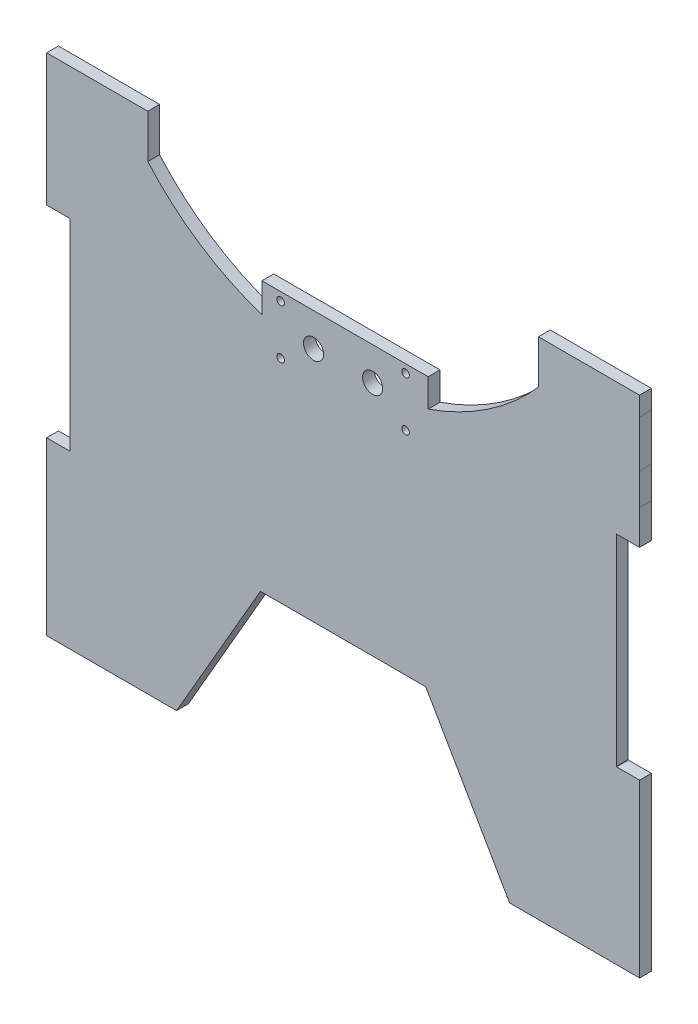
SolidWorks part; units mm, degrees
ref_plane "Front Plane" through (0, 0, 0) normal (0, 0, 1) x (1, 0, 0)
ref_plane "Top Plane" through (0, 0, 0) normal (0, 1, 0) x (1, 0, 0)
ref_plane "Right Plane" through (0, 0, 0) normal (1, 0, 0) x (0, 0, -1)
sketch "Sketch1" plane through (0, 0, 0) normal (0, 0, 1) x (1, 0, 0)
  line L0 (-91.7228, 104.3562) -> (-126.4585, 104.3562)
  line L1 (-126.4585, 104.3562) -> (-126.4753, 84.6144)
  line L2 (-126.4753, 84.6144) -> (-126.4804, 71.1807)
  line L3 (-126.4804, 71.1807) -> (-126.4807, 56.5595)
  line L4 (-126.4807, 56.5595) -> (-116.6382, 56.5595)
  line L5 (-116.6382, 56.5595) -> (-116.6382, -28.7876)
  line L6 (-116.6382, -28.7876) -> (-126.4819, -28.7876)
  line L7 (-126.4819, -28.7876) -> (-126.4819, -101.3441)
  line L8 (-126.4819, -101.3441) -> (-71.449, -101.3441)
  line L9 (-71.449, -101.3441) -> (-35.9282, -39.8203)
  line L10 (-35.9282, -39.8203) -> (34.0758, -39.8203)
  line L11 (34.0758, -39.8203) -> (69.5966, -101.3441)
  line L12 (69.5966, -101.3441) -> (124.6295, -101.3441)
  line L13 (124.6295, -101.3441) -> (124.6295, -28.7876)
  line L14 (124.6295, -28.7876) -> (114.9127, -28.7876)
  line L15 (114.7857, -28.6606) -> (114.7857, 56.4325)
  line L16 (114.9127, 56.5595) -> (124.6283, 56.5595)
  line L17 (124.6283, 56.5595) -> (124.6279, 71.1707)
  line L18 (124.6279, 71.1707) -> (124.6228, 84.6244)
  line L19 (124.6228, 84.6244) -> (124.6061, 104.3562)
  line L20 (124.6061, 104.3562) -> (89.8704, 104.3562)
  line L21 (35.0896, 62.5159) -> (35.0896, 40.386)
  line L22 (35.0896, 40.386) -> (-35.3107, 40.386)
  line L23 (-35.3107, 40.386) -> (-35.3107, 61.9649)
  arc A0 (-91.7228, 104.3562) -> (-35.3107, 61.9649) centre (-0.9262, 166.4527) ccw
  arc A1 (114.7857, -28.6606) -> (114.9127, -28.7876) centre (114.9127, -28.6606) ccw
  arc A2 (114.9127, 56.5595) -> (114.7857, 56.4325) centre (114.9127, 56.4325) ccw
  arc A3 (35.0896, 62.5159) -> (89.8704, 104.3562) centre (-0.9262, 166.4527) ccw
extrude "Boss-Extrude1" add sketch "Sketch1" along normal blind 5
sketch "Sketch2" plane through (0, 0, 5) normal (0, 0, 1) x (1, 0, 0)
  line L1 (-35.3107, 40.386) -> (35.0896, 40.386)
  line L2 (-35.3107, 40.386) -> (-35.3107, 74.386)
  line L3 (-35.3107, 74.386) -> (35.0896, 74.386)
  line L4 (35.0896, 40.386) -> (35.0896, 74.386)
  line L5 (-35.3107, 40.386) -> (35.0896, 74.386) construction
  line L6 (-35.3107, 74.386) -> (35.0896, 40.386) construction
  circle A0 centre (-27.3907, 70.8504) radius 1.6
  circle A1 centre (-27.3907, 49.9215) radius 1.6
  circle A2 centre (25.5383, 49.9215) radius 1.6
  circle A3 centre (25.5383, 70.8504) radius 1.6
  circle A4 centre (-13.4262, 60.386) radius 4.25
  circle A5 centre (11.5738, 60.386) radius 4.25
  point P4 (-0.1106, 57.386)
  dimension "D1" = 8.5
extrude "Boss-Extrude2" add sketch "Sketch2" against normal blind 5
sketch "Sketch3" plane through (0, 0, 5) normal (0, 0, 1) x (1, 0, 0)
  line L0 (-126.4585, 104.3562) -> (-126.4585, 112.386)
  line L1 (-91.7228, 104.3562) -> (-91.7228, 112.386)
  line L2 (-126.4585, 112.386) -> (-66.5142, 112.386) construction
  line L3 (-91.7228, 112.386) -> (-126.4585, 112.386)
  line L4 (-0.9262, 108.4013) -> (-0.9262, 130.7418) construction
  line L5 (89.8704, 104.3562) -> (124.6061, 104.3562)
  line L6 (89.8704, 112.386) -> (124.6061, 112.386)
  line L7 (89.8704, 104.3562) -> (89.8704, 112.386)
  line L8 (124.6061, 104.3562) -> (124.6061, 112.386)
  line L24 (-35.3107, 74.386) -> (-35.3107, 61.9649)
  line L25 (-91.7228, 104.3562) -> (-126.4585, 104.3562)
  line L26 (-126.4585, 104.3562) -> (-126.4753, 84.6144)
  line L27 (-126.4753, 84.6144) -> (-126.4804, 71.1807)
  line L28 (-126.4804, 71.1807) -> (-126.4807, 56.5595)
  line L29 (-126.4807, 56.5595) -> (-116.6382, 56.5595)
  line L30 (-116.6382, 56.5595) -> (-116.6382, -28.7876)
  line L31 (-116.6382, -28.7876) -> (-126.4819, -28.7876)
  line L32 (-126.4819, -28.7876) -> (-126.4819, -101.3441)
  line L33 (-126.4819, -101.3441) -> (-71.449, -101.3441)
  line L34 (-71.449, -101.3441) -> (-35.9282, -39.8203)
  line L35 (-35.9282, -39.8203) -> (34.0758, -39.8203)
  line L36 (34.0758, -39.8203) -> (69.5966, -101.3441)
  line L37 (69.5966, -101.3441) -> (124.6295, -101.3441)
  line L38 (124.6295, -101.3441) -> (124.6295, -28.7876)
  line L39 (124.6295, -28.7876) -> (114.9127, -28.7876)
  line L40 (114.7857, -28.6606) -> (114.7857, 56.4325)
  line L41 (114.9127, 56.5595) -> (124.6283, 56.5595)
  line L42 (124.6283, 56.5595) -> (124.6279, 71.1707)
  line L43 (124.6279, 71.1707) -> (124.6228, 84.6244)
  line L44 (124.6228, 84.6244) -> (124.6061, 104.3562)
  line L45 (124.6061, 104.3562) -> (89.8704, 104.3562)
  line L46 (35.0896, 62.5159) -> (35.0896, 74.386)
  line L47 (35.0896, 74.386) -> (-35.3107, 74.386)
  line L49 (-91.7228, 104.3562) -> (-126.4585, 104.3562)
  line L69 (124.6061, 104.3562) -> (89.8704, 104.3562)
  arc A4 (-91.7228, 104.3562) -> (-35.3107, 61.9649) centre (-0.9262, 166.4527) ccw
  arc A5 (114.7857, -28.6606) -> (114.9127, -28.7876) centre (114.9127, -28.6606) ccw
  arc A6 (114.9127, 56.5595) -> (114.7857, 56.4325) centre (114.9127, 56.4325) ccw
  arc A7 (35.0896, 62.5159) -> (89.8704, 104.3562) centre (-0.9262, 166.4527) ccw
  line M32 (-91.7228, 104.3562) -> (-126.4585, 104.3562)
  line M54 (124.6061, 104.3562) -> (89.8704, 104.3562)
  dimension "D1" = 0
extrude "Boss-Extrude3" add sketch "Sketch3" against normal blind 5 contours L1 L3 L0 M32 | L8 L6 L7 M54
sketch "Sketch4" plane through (0, 0, 5) normal (0, 0, 1) x (1, 0, 0)
  line L0 (89.8704, 112.386) -> (81.7857, 112.386)
  line L1 (81.7857, 112.386) -> (81.7857, 93.9356)
  line L2 (89.8704, 112.386) -> (89.8704, 104.3562)
  line L3 (-0.9262, -39.8203) -> (-0.9262, -74.9182) construction
  line L4 (-35.9282, -39.8203) -> (34.0758, -39.8203) construction
  line L5 (-91.7228, 112.386) -> (-91.7228, 104.3562)
  line L6 (-83.6382, 112.386) -> (-83.6382, 93.9356)
  line L7 (-91.7228, 112.386) -> (-83.6382, 112.386)
  arc A0 (35.0896, 62.5159) -> (89.8704, 104.3562) centre (-0.9262, 166.4527) ccw construction
  arc A1 (81.7857, 93.9356) -> (89.8704, 104.3562) centre (-0.9262, 166.4527) ccw
  arc A2 (-91.7228, 104.3562) -> (-35.3107, 61.9649) centre (-0.9262, 166.4527) ccw construction
  arc A3 (-91.7228, 104.3562) -> (-83.6382, 93.9356) centre (-0.9262, 166.4527) ccw
extrude "Boss-Extrude4" add sketch "Sketch4" against normal blind 5
